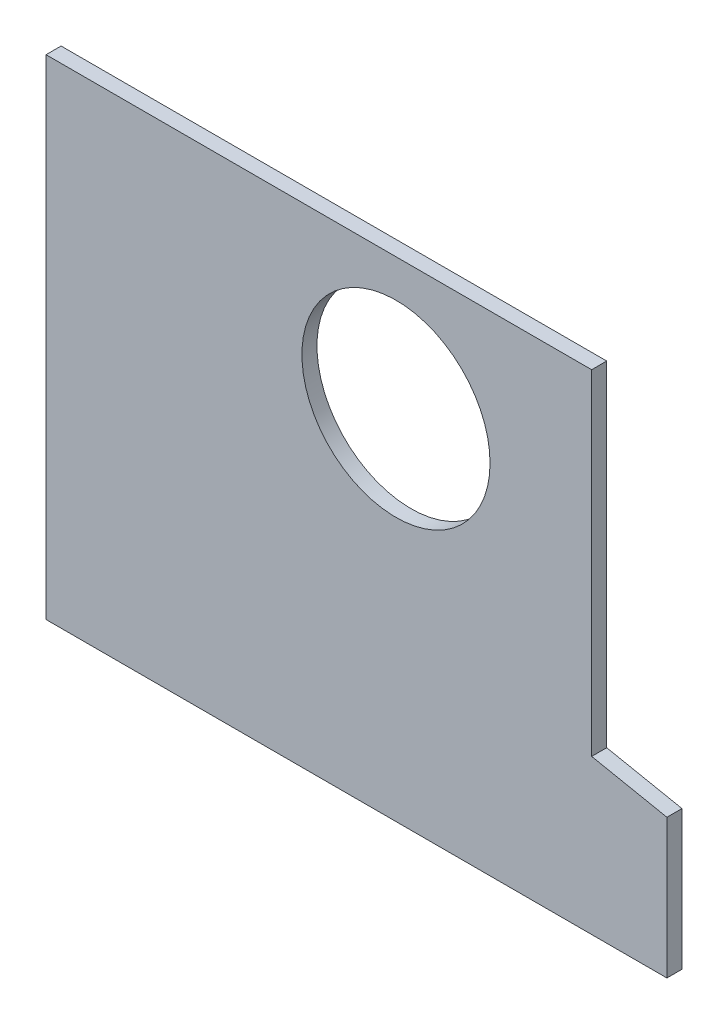
SolidWorks part; units mm, degrees
material "Maple"
ref_plane "Front Plane" through (0, 0, 0) normal (0, 0, 1) x (1, 0, 0)
ref_plane "Top Plane" through (0, 0, 0) normal (0, 1, 0) x (1, 0, 0)
ref_plane "Right Plane" through (0, 0, 0) normal (1, 0, 0) x (0, 0, -1)
sketch "Sketch1" plane through (0, 0, 0) normal (0, 0, 1) x (1, 0, 0)
  line L0 (-82.5, 0) -> (82.5, 0)
  line L1 (-82.5, 0) -> (-82.5, 130)
  line L2 (-82.5, 130) -> (62.5, 130)
  line L3 (62.5, 130) -> (62.5, 41)
  line L4 (62.5, 41) -> (82.5, 37)
  line L5 (82.5, 37) -> (82.5, 0)
  circle A0 centre (10.5, 95) radius 25
  point P4 (0, 0)
  dimension "D7" = 50
  dimension "D1" = 165
  dimension "D2" = 130
  dimension "D3" = 145
  dimension "D4" = 89
  dimension "D5" = 37
  dimension "D6" = 35
  dimension "D8" = 52
extrude "Boss-Extrude1" add sketch "Sketch1" along normal blind 4
